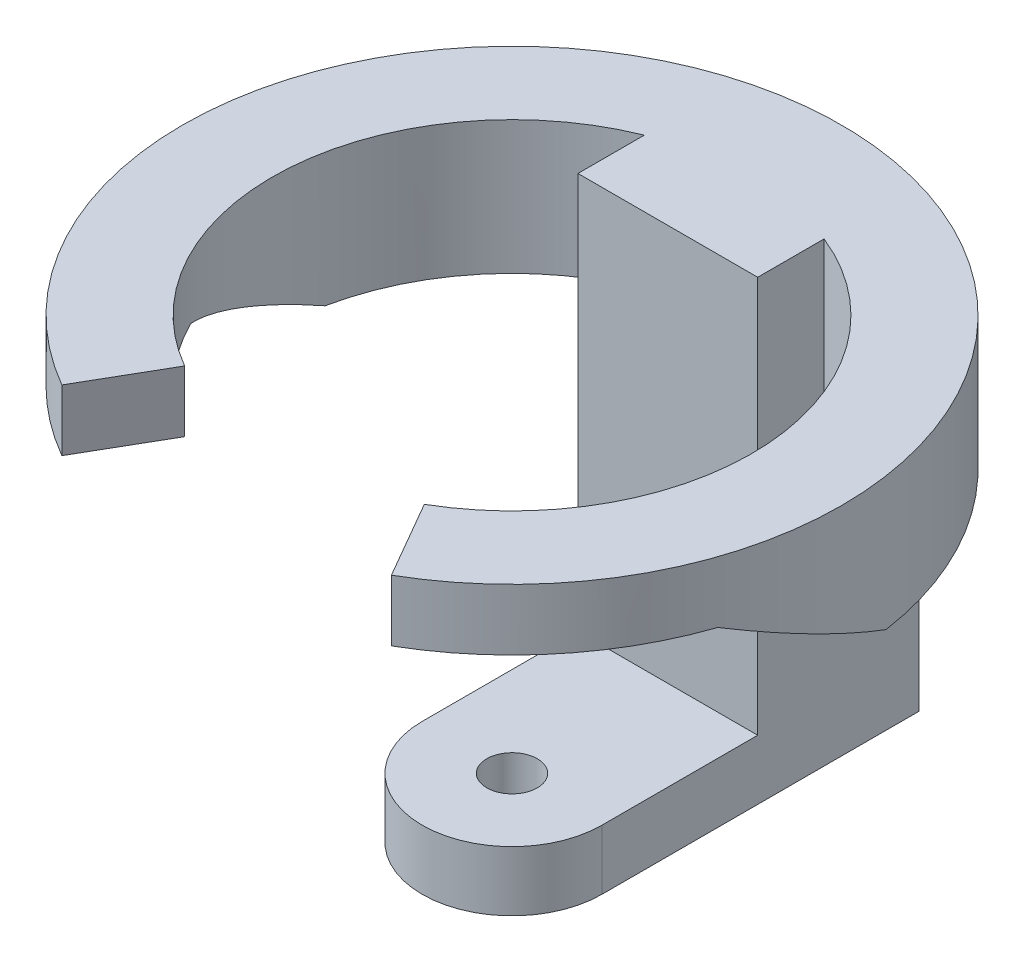
SolidWorks part; units mm, degrees
ref_plane "Front Plane" through (0, 0, 0) normal (0, 0, 1) x (1, 0, 0)
ref_plane "Top Plane" through (0, 0, 0) normal (0, 1, 0) x (1, 0, 0)
ref_plane "Right Plane" through (0, 0, 0) normal (1, 0, 0) x (0, 0, -1)
ref_axis "Axis1" through (0, 80.01, 0) along (0, -1, 0)
sketch "Sketch1" plane through (0, 0, 0) normal (0, 1, 0) x (1, 0, 0)
  line L0 (15, 0) -> (15, 52.915)
  line L2 (-15, 52.915) -> (-15, 0)
  arc A0 (-15, 0) -> (15, 0) centre (0, 0) ccw
  arc A1 (15, 52.915) -> (-15, 52.915) centre (0, 0) ccw
  dimension "D1" = 15
  dimension "D2" = 55
extrude "Boss-Extrude1" add sketch "Sketch1" along normal blind 10
sketch "Sketch2" plane through (0, 10, 0) normal (0, 1, 0) x (1, 0, 0)
  line L0 (-15, 52.915) -> (-15, 0) construction
  line L1 (-15, 26) -> (15, 26)
  line L2 (15, 0) -> (15, 52.915) construction
  line L3 (15, 26) -> (15, 52.915)
  line L4 (-15, 26) -> (-15, 52.915)
  arc A0 (15, 52.915) -> (-15, 52.915) centre (0, 0) ccw construction
  arc A1 (15, 52.915) -> (-15, 52.915) centre (0, 0) ccw
  dimension "D1" = 26
extrude "Boss-Extrude2" add sketch "Sketch2" along normal blind 76.2 from surface at -10 starting at plane "Top Plane"
sketch "Sketch3" plane through (0, 0, 0) normal (1, 0, 0) x (0, 0, -1)
  line L0 (55, 0) -> (55, 76.2) construction
  line L1 (40, 76.2) -> (55, 76.2)
  line L2 (40, 76.2) -> (40, 53.975)
  line L3 (40, 53.975) -> (55, 53.975)
  line L4 (55, 76.2) -> (55, 53.975)
  line L5 (26, 76.2) -> (52.915, 76.2) construction
  dimension "D1" = 53.975
  dimension "D2" = 15
revolve "Revolve1" add sketch "Sketch3" angle 300 mid plane about axis through (0, 80.01, 0) along (0, -1, 0)
sketch "Sketch4" plane through (0, 0, 0) normal (1, 0, 0) x (0, 0, -1)
  line L0 (8, 53.975) -> (-17.7341, 65.975)
  line L1 (-47.6314, 53.975) -> (52.915, 53.975) construction
  line L2 (-17.7341, 65.975) -> (-47.6314, 65.975)
  line L3 (-47.6314, 53.975) -> (-47.6314, 76.2) construction
  line L4 (-47.6314, 65.975) -> (-47.6314, 53.975)
  line L5 (-47.6314, 53.975) -> (8, 53.975)
  line L6 (0, 80.01) -> (0, -3.81) construction
  dimension "D1" = 25
  dimension "D2" = 12
  dimension "D3" = 8
extrude "Cut-Extrude1" cut sketch "Sketch4" against normal through all and the other way through all
hole_wizard "3/8-24 Tapped Hole1" positions "Sketch5" profile "Sketch7" tap size "3/8-24" standard "ANSI Inch" end condition through all
sketch "Sketch5" plane through (0, 10, 0) normal (0, 1, 0) x (1, 0, 0)
  point P0 (0, 0)
sketch "Sketch7" plane through (0, 10, 0) normal (1, 0, 0) x (0, 0, 1)
  line L0 (0, 0) -> (0, 10)
  line L1 (0, 10) -> (4.2164, 10)
  line L2 (4.2164, 10) -> (4.2164, 0)
  line L5 (4.2164, 0) -> (0, 0)
  line L11 (0, -6.35) -> (0, 107.95) construction
  dimension "Thru Tap Drill Dia." = 8.4328
  dimension "Thru Tap Drill Depth" = 10
cosmetic thread "Hole Thread1" parameters "D2"=9.525
